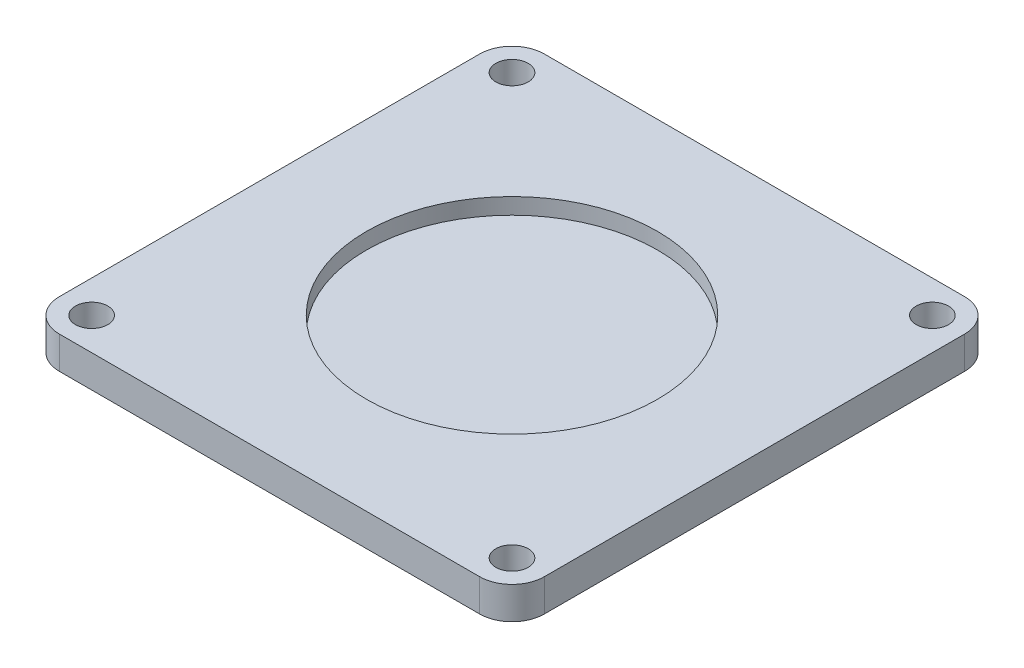
SolidWorks part; units mm, degrees
ref_plane "Front Plane" through (0, 0, 0) normal (0, 0, 1) x (1, 0, 0)
ref_plane "Top Plane" through (0, 0, 0) normal (0, 1, 0) x (1, 0, 0)
ref_plane "Right Plane" through (0, 0, 0) normal (1, 0, 0) x (0, 0, -1)
sketch "Sketch1" plane through (0, 0, 0) normal (0, 1, 0) x (1, 0, 0)
  line L1 (-15, 15) -> (15, 15)
  line L2 (-15, 15) -> (-15, -15)
  line L3 (-15, -15) -> (15, -15)
  line L4 (15, 15) -> (15, -15)
  point P0 (0, 0)
  dimension "D1" = 30
  dimension "D2" = 30
extrude "Boss-Extrude1" add sketch "Sketch1" along normal blind 2
sketch "Sketch2" plane through (0, 2, 0) normal (0, 1, 0) x (1, 0, 0)
  circle A0 centre (0, 0) radius 9
  dimension "D1" = 18
extrude "Cut-Extrude1" cut sketch "Sketch2" against normal blind 1
sketch "Sketch3" plane through (0, 0, 0) normal (0, -1, 0) x (1, 0, 0)
  circle A0 centre (0, 0) radius 10
  dimension "D1" = 20
extrude "Boss-Extrude2" add sketch "Sketch3" along normal blind 3
sketch "Sketch4" plane through (0, -3, 0) normal (0, -1, 0) x (1, 0, 0)
  circle A0 centre (0, 0) radius 1
  dimension "D1" = 2
extrude "Boss-Extrude3" add sketch "Sketch4" along normal blind 3
fillet "Fillet1" radius 1 1 edges at (0, -3, -10)
chamfer "Chamfer2" distance 0.5 angle 10 1 edges at (0, -6, -1)
sketch "Sketch5" plane through (0, 0, 0) normal (0, -1, 0) x (1, 0, 0)
  line L0 (-15, 15) -> (15, 15) construction
  line L2 (-15, -15) -> (-15, 15) construction
  line L3 (15, 15) -> (15, -15) construction
  line L4 (15, -15) -> (-15, -15) construction
  circle A0 centre (-13, 13) radius 1
  circle A1 centre (13, 13) radius 1
  circle A2 centre (13, -13) radius 1
  circle A3 centre (-13, -13) radius 1
  point P10 (0, 0)
  point P12 (-15, 12.5563)
  point P18 (0, 0)
  dimension "D1" = 2
  dimension "D2" = 2
  dimension "D3" = 2
  dimension "D4" = 2
  dimension "D5" = 2
  dimension "D6" = 2
  dimension "D7" = 2
  dimension "D8" = 2
  dimension "D9" = 2
  dimension "D10" = 2
  dimension "D11" = 2
  dimension "D12" = 2
extrude "Cut-Extrude2" cut sketch "Sketch5" against normal through all contours A0 | A3 | A2 | A1
fillet "Fillet2" radius 2 4 edges at (-15, 1, -15) (-15, 1, 15) (15, 1, 15) (15, 1, -15)
